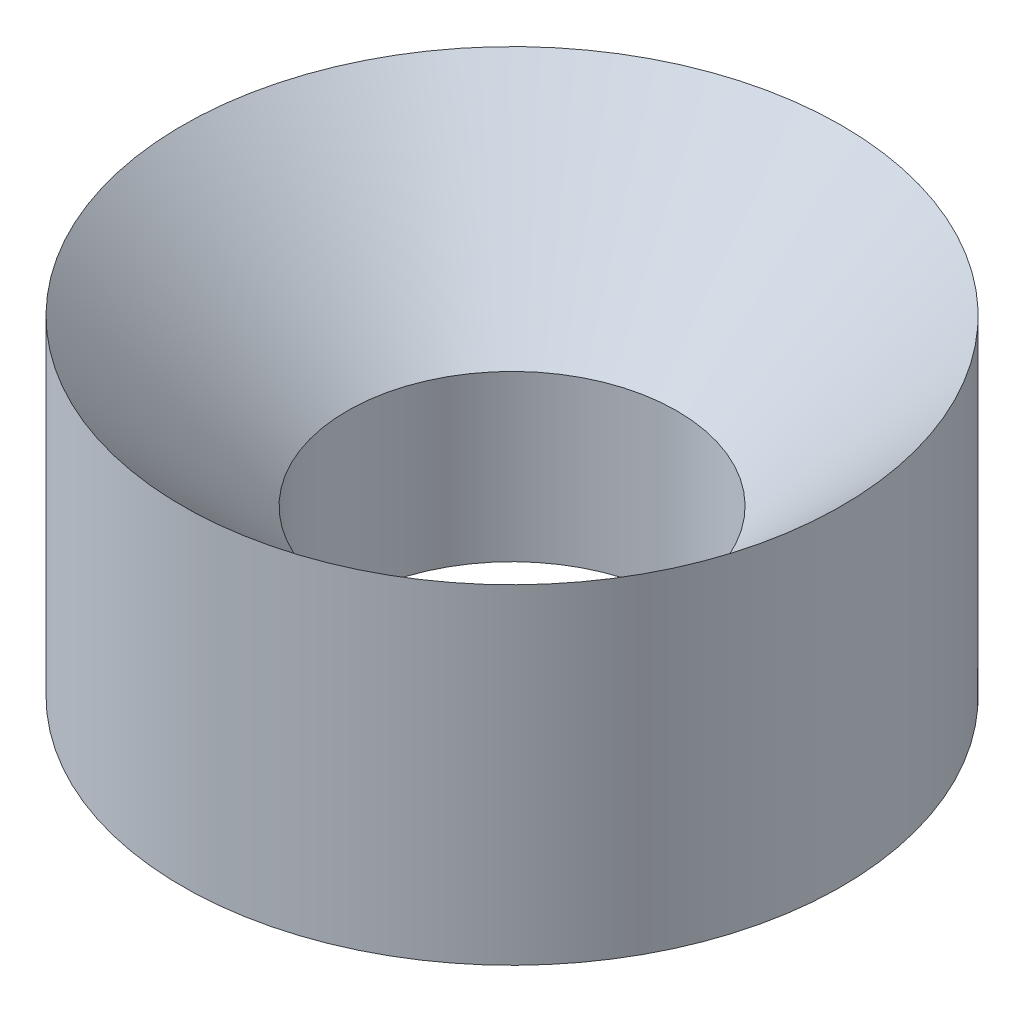
SolidWorks part; units mm, degrees
ref_plane "Спереди" through (0, 0, 0) normal (0, 0, 1) x (1, 0, 0)
ref_plane "Сверху" through (0, 0, 0) normal (0, 1, 0) x (1, 0, 0)
ref_plane "Справа" through (0, 0, 0) normal (1, 0, 0) x (0, 0, -1)
other "Configuration Table"
sketch "Sketch3" plane through (0, 0, 0) normal (1, 0, 0) x (0, 0, -1)
  line L0 (0, 0) -> (0, 40)
  line L1 (0, 0) -> (-20, 0)
  line L2 (-20, 0) -> (-20, 20)
  line L3 (-20, 20) -> (0, 40)
  line L4 (-40, 0) -> (-40, 46.093) construction
  dimension "D1" = 40
  dimension "D2" = 20
  dimension "D3" = 20
  dimension "D4" = 20
revolve "Revolve1" add sketch "Sketch3" angle 360 about L4
